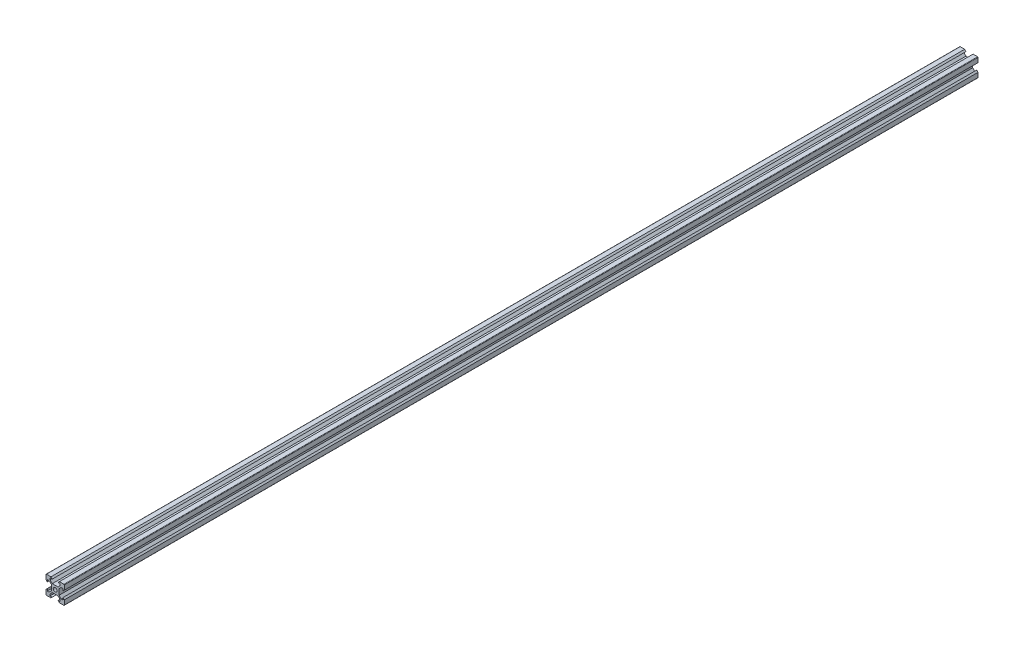
SolidWorks part; units mm, degrees
ref_plane "Front Plane" through (0, 0, 0) normal (0, 0, 1) x (1, 0, 0)
ref_plane "Top Plane" through (0, 0, 0) normal (0, 1, 0) x (1, 0, 0)
ref_plane "Right Plane" through (0, 0, 0) normal (1, 0, 0) x (0, 0, -1)
sketch "Sketch1" plane through (0, 0, 0) normal (0, 0, 1) x (1, 0, 0)
  line L0 (-3.125, 4.245) -> (3.125, 4.245)
  line L1 (3.125, 4.245) -> (5.5, 6.62)
  line L2 (5.5, 6.62) -> (5.5, 8.545)
  line L3 (5.5, 8.545) -> (3.125, 8.545)
  line L4 (3.125, 8.545) -> (4.58, 10)
  line L5 (4.58, 10) -> (9.5, 10)
  line L6 (10, 9.5) -> (10, 4.58)
  line L7 (10, 4.58) -> (8.545, 3.125)
  line L8 (8.545, 3.125) -> (8.545, 5.5)
  line L9 (8.545, 5.5) -> (6.62, 5.5)
  line L10 (6.62, 5.5) -> (4.245, 3.125)
  line L11 (4.245, 3.125) -> (4.245, -3.125)
  line L12 (0, 0) -> (-9.4136, 0) construction
  line L13 (0, 0) -> (0, -8.8273) construction
  line L14 (-4.245, 3.125) -> (-4.245, -3.125)
  line L15 (-6.62, 5.5) -> (-4.245, 3.125)
  line L16 (-8.545, 5.5) -> (-6.62, 5.5)
  line L17 (-8.545, 3.125) -> (-8.545, 5.5)
  line L18 (-10, 4.58) -> (-8.545, 3.125)
  line L19 (-10, 9.5) -> (-10, 4.58)
  line L20 (-4.58, 10) -> (-9.5, 10)
  line L21 (-3.125, 8.545) -> (-4.58, 10)
  line L22 (-5.5, 8.545) -> (-3.125, 8.545)
  line L23 (-5.5, 6.62) -> (-5.5, 8.545)
  line L24 (-3.125, 4.245) -> (-5.5, 6.62)
  line L25 (-3.125, -4.245) -> (-5.5, -6.62)
  line L26 (-5.5, -6.62) -> (-5.5, -8.545)
  line L27 (-5.5, -8.545) -> (-3.125, -8.545)
  line L28 (-3.125, -8.545) -> (-4.58, -10)
  line L29 (-4.58, -10) -> (-9.5, -10)
  line L30 (-10, -9.5) -> (-10, -4.58)
  line L31 (-10, -4.58) -> (-8.545, -3.125)
  line L32 (-8.545, -3.125) -> (-8.545, -5.5)
  line L33 (-8.545, -5.5) -> (-6.62, -5.5)
  line L34 (-6.62, -5.5) -> (-4.245, -3.125)
  line L35 (6.62, -5.5) -> (4.245, -3.125)
  line L36 (8.545, -5.5) -> (6.62, -5.5)
  line L37 (8.545, -3.125) -> (8.545, -5.5)
  line L38 (10, -4.58) -> (8.545, -3.125)
  line L39 (10, -9.5) -> (10, -4.58)
  line L40 (4.58, -10) -> (9.5, -10)
  line L41 (3.125, -8.545) -> (4.58, -10)
  line L42 (5.5, -8.545) -> (3.125, -8.545)
  line L43 (5.5, -6.62) -> (5.5, -8.545)
  line L44 (3.125, -4.245) -> (5.5, -6.62)
  line L45 (-3.125, -4.245) -> (3.125, -4.245)
  circle A0 centre (0, 0) radius 2.1
  arc A1 (10, 9.5) -> (9.5, 10) centre (9.5, 9.5) ccw
  arc A2 (-10, 9.5) -> (-9.5, 10) centre (-9.5, 9.5) cw
  arc A3 (-10, -9.5) -> (-9.5, -10) centre (-9.5, -9.5) ccw
  arc A4 (10, -9.5) -> (9.5, -10) centre (9.5, -9.5) cw
  point P3 (-10, 10)
  point P18 (10, 10)
  point P35 (0, 4.245)
  point P37 (4.245, 0)
  point P38 (-4.245, 0)
  point P62 (0, -4.245)
  point P63 (10, -10)
  point P64 (-10, -10)
  dimension "D1" = 4.2
  dimension "D17" = 0.5
  dimension "D2" = 10
  dimension "D3" = 10
  dimension "D4" = 45
  dimension "D5" = 3.125
  dimension "D6" = 3.125
  dimension "D7" = 4.58
  dimension "D8" = 4.58
  dimension "D9" = 5.5
  dimension "D10" = 5.5
  dimension "D13" = 3.125
  dimension "D14" = 3.125
  dimension "D15" = 4.3
  dimension "D16" = 4.3
extrude "Boss-Extrude1" add sketch "Sketch1" along normal blind 1000
